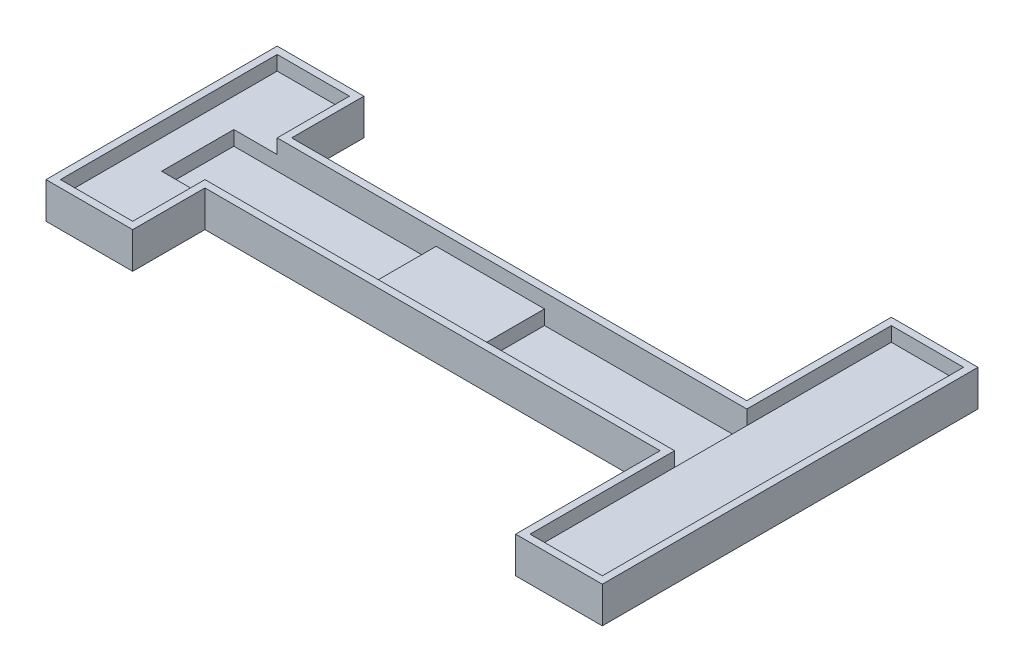
SolidWorks part; units mm, degrees
ref_plane "前视基准面" through (0, 0, 0) normal (0, 0, 1) x (1, 0, 0)
ref_plane "上视基准面" through (0, 0, 0) normal (0, 1, 0) x (1, 0, 0)
ref_plane "右视基准面" through (0, 0, 0) normal (1, 0, 0) x (0, 0, -1)
other "Configuration Table"
sketch "草图1" plane through (0, 0, 0) normal (0, 1, 0) x (1, 0, 0)
  line L0 (0, 0) -> (19, 0) construction
  line L1 (-14, -5) -> (14, -5)
  line L2 (-14, -5) -> (-14, 5)
  line L3 (-14, 5) -> (14, 5)
  line L4 (14, -5) -> (14, 5)
  line L5 (-14, -5) -> (14, 5) construction
  line L6 (-14, 5) -> (14, -5) construction
  line L7 (24, -25) -> (14, -25)
  line L8 (24, -25) -> (24, 25)
  line L9 (24, 25) -> (14, 25)
  line L10 (14, -25) -> (14, 25)
  line L11 (24, -25) -> (14, 25) construction
  line L12 (24, 25) -> (14, -25) construction
  line L13 (0, 0) -> (-21.5, 0) construction
  line L14 (-21.5, 0) -> (-43, 0) construction
  line L15 (-56, 0) -> (-43, 0)
  line L16 (-29, 5) -> (-14, 5)
  line L17 (-29, 5) -> (-29, -5)
  line L18 (-29, -5) -> (-14, -5)
  line L19 (-14, 5) -> (-14, -5)
  line L20 (-29, 5) -> (-14, -5) construction
  line L21 (-29, -5) -> (-14, 5) construction
  line L22 (-57, -5) -> (-29, -5)
  line L23 (-57, -5) -> (-57, 5)
  line L24 (-57, 5) -> (-29, 5)
  line L25 (-29, -5) -> (-29, 5)
  line L26 (-57, -5) -> (-29, 5) construction
  line L27 (-57, 5) -> (-29, -5) construction
  line L36 (-51, -15) -> (-61, -15)
  line L37 (-51, -15) -> (-51, 15)
  line L38 (-51, 15) -> (-61, 15)
  line L39 (-61, -15) -> (-61, 15)
  line L40 (-51, -15) -> (-61, 15) construction
  line L41 (-51, 15) -> (-61, -15) construction
  point P0 (0, 0)
  point P6 (19, 0)
  point P13 (-56, 0)
  dimension "D1" = 28
  dimension "D2" = 10
  dimension "D3" = 10
  dimension "D4" = 50
  dimension "D5" = 15
  dimension "D6" = 28
  dimension "D7" = 10
  dimension "D8" = 6
  dimension "D9" = 30
sketch "草图2" plane through (0, 0, 0) normal (0, 1, 0) x (1, 0, 0)
  line L1 (-61, 15) -> (-51, 15)
  line L2 (-61, 15) -> (-61, -15)
  line L3 (-61, -15) -> (-51, -15)
  line L4 (-51, 15) -> (-51, -15)
  line L5 (-57, 5) -> (14, 5)
  line L6 (-57, 5) -> (-57, -5)
  line L7 (-57, -5) -> (14, -5)
  line L8 (14, 5) -> (14, -5)
  line L9 (24, -25) -> (14, -25)
  line L10 (24, -25) -> (24, 25)
  line L11 (24, 25) -> (14, 25)
  line L12 (14, -25) -> (14, 25)
extrude "凸台-拉伸1" add sketch "草图2" along normal blind 1 contours L8 L5 L4 L7 | L6 L7 L4 L5 | L7 L6 L5 L4 L1 L2 L3 | L12 L9 L10 L11 L8
sketch "草图4" plane through (0, 1, 0) normal (0, 1, 0) x (1, 0, 0)
  line L0 (-50, -16) -> (-50, -6)
  line L1 (-50, -6) -> (13, -6)
  line L2 (13, -6) -> (13, -26)
  line L3 (13, -26) -> (25, -26)
  line L4 (25, -26) -> (25, 26)
  line L5 (25, 26) -> (13, 26)
  line L6 (13, 26) -> (13, 6)
  line L7 (13, 6) -> (-50, 6)
  line L8 (-50, 6) -> (-50, 16)
  line L9 (-50, 16) -> (-62, 16)
  line L10 (-62, 16) -> (-62, -16)
  line L11 (-62, -16) -> (-50, -16)
  line L12 (-51, -15) -> (-51, -5)
  line L13 (-51, -5) -> (14, -5)
  line L14 (14, -5) -> (14, -25)
  line L15 (14, -25) -> (24, -25)
  line L16 (24, -25) -> (24, 25)
  line L17 (24, 25) -> (14, 25)
  line L18 (14, 25) -> (14, 5)
  line L19 (14, 5) -> (-51, 5)
  line L20 (-51, 5) -> (-51, 15)
  line L21 (-51, 15) -> (-61, 15)
  line L22 (-61, 15) -> (-61, -15)
  line L23 (-61, -15) -> (-51, -15)
  line L24 (-51, -15) -> (-51, -5)
  line L25 (-51, -5) -> (14, -5)
  line L26 (14, -5) -> (14, -25)
  line L27 (14, -25) -> (24, -25)
  line L28 (24, -25) -> (24, 25)
  line L29 (24, 25) -> (14, 25)
  line L30 (14, 25) -> (14, 5)
  line L31 (14, 5) -> (-51, 5)
  line L32 (-51, 5) -> (-51, 15)
  line L33 (-51, 15) -> (-61, 15)
  line L34 (-61, 15) -> (-61, -15)
  line L35 (-61, -15) -> (-51, -15)
  dimension "D1" = 0
  dimension "D2" = 1
extrude "凸台-拉伸2" add sketch "草图4" along normal blind 4 and the other way blind 1
sketch "草图5" plane through (0, 1, 0) normal (0, 1, 0) x (1, 0, 0)
  line L0 (-57, 5) -> (-57, -5)
  line L1 (-29, 5) -> (-14, 5)
  line L2 (-29, 5) -> (-29, -5)
  line L3 (-29, -5) -> (-14, -5)
  line L4 (-14, 5) -> (-14, -5)
  line L5 (14, 25) -> (24, 25)
  line L6 (14, 25) -> (14, -25)
  line L7 (14, -25) -> (24, -25)
  line L8 (24, 25) -> (24, -25)
  line L9 (-57, -5) -> (-51, -5)
  line L10 (-51, -5) -> (-51, -15)
  line L11 (-51, -15) -> (-61, -15)
  line L12 (-61, -15) -> (-61, 15)
  line L13 (-61, 15) -> (-51, 15)
  line L14 (-51, 15) -> (-51, 5)
  line L15 (-51, 5) -> (-57, 5)
extrude "凸台-拉伸3" add sketch "草图5" along normal blind 2
